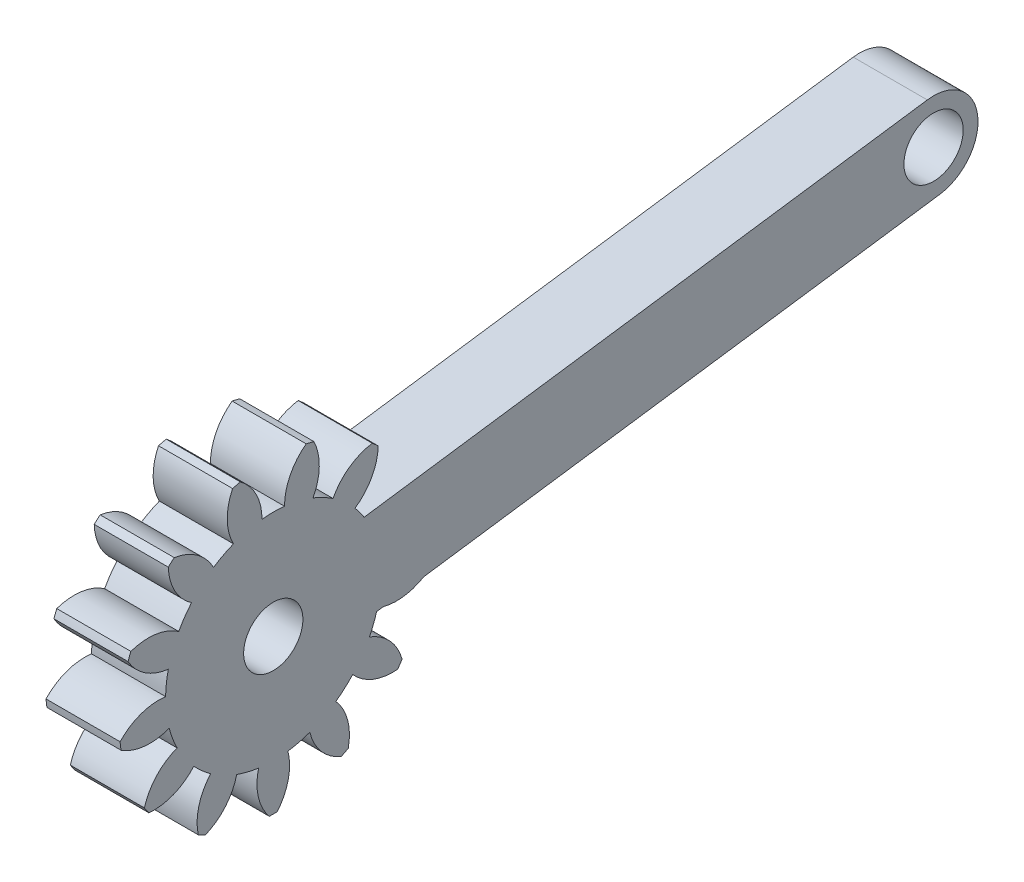
SolidWorks part; units mm, degrees
ref_plane "Front Plane" through (0, 0, 0) normal (0, 0, 1) x (1, 0, 0)
ref_plane "Top Plane" through (0, 0, 0) normal (0, 1, 0) x (1, 0, 0)
ref_plane "Right Plane" through (0, 0, 0) normal (1, 0, 0) x (0, 0, -1)
ref_plane "Plane1" through (-2.7128, 0, 0) normal (1, 0, 0) x (0, 0, -1)
sketch "Sketch1" plane through (-2.7128, 0, 0) normal (1, 0, 0) x (0, 0, -1)
  circle A0 centre (-74.3928, 33.7527) radius 2
  arc A1 (-81.4756, 41.3436) -> (-79.9078, 38.4838) centre (-77.8783, 41.4561) ccw
  arc A2 (-79.9078, 38.4838) -> (-80.7721, 37.2317) centre (-74.3928, 33.7527) ccw
  arc A3 (-80.7721, 37.2317) -> (-84.0021, 37.6835) centre (-82.8316, 34.28) ccw
  arc A4 (-84.0021, 37.6835) -> (-84.192, 37.1826) centre (-74.3928, 33.7527) ccw
  arc A5 (-84.192, 37.1826) -> (-81.4748, 35.3789) centre (-81.059, 38.9539) ccw
  arc A6 (-81.4748, 35.3789) -> (-81.6582, 33.8686) centre (-74.3928, 33.7527) ccw
  arc A7 (-81.6582, 33.8686) -> (-84.7281, 32.7676) centre (-82.11, 30.2979) ccw
  arc A8 (-84.7281, 32.7676) -> (-84.6635, 32.2358) centre (-74.3928, 33.7527) ccw
  arc A9 (-84.6635, 32.2358) -> (-81.4193, 31.9015) centre (-82.7125, 35.2603) ccw
  arc A10 (-81.4193, 31.9015) -> (-80.8798, 30.4789) centre (-74.3928, 33.7527) ccw
  arc A11 (-80.8798, 30.4789) -> (-83.0864, 28.0774) centre (-79.6205, 27.1073) ccw
  arc A12 (-83.0864, 28.0774) -> (-82.7821, 27.6366) centre (-74.3928, 33.7527) ccw
  arc A13 (-82.7821, 27.6366) -> (-79.7542, 28.8482) centre (-82.4602, 31.2212) ccw
  arc A14 (-79.7542, 28.8482) -> (-78.6154, 27.8393) centre (-74.3928, 33.7527) ccw
  arc A15 (-78.6154, 27.8393) -> (-79.4532, 24.6874) centre (-75.9334, 25.4391) ccw
  arc A16 (-79.4532, 24.6874) -> (-78.9789, 24.4384) centre (-74.3928, 33.7527) ccw
  arc A17 (-78.9789, 24.4384) -> (-76.8608, 26.9185) centre (-80.3597, 27.7621) ccw
  arc A18 (-76.8608, 26.9185) -> (-75.3836, 26.5543) centre (-74.3928, 33.7527) ccw
  arc A19 (-75.3836, 26.5543) -> (-74.6607, 23.3741) centre (-71.8934, 25.6754) ccw
  arc A20 (-74.6607, 23.3741) -> (-74.125, 23.3741) centre (-74.3928, 33.7527) ccw
  arc A21 (-74.125, 23.3741) -> (-73.4021, 26.5543) centre (-76.8923, 25.6754) ccw
  arc A22 (-73.4021, 26.5543) -> (-71.9249, 26.9185) centre (-74.3928, 33.7527) ccw
  arc A23 (-71.9249, 26.9185) -> (-69.8068, 24.4384) centre (-68.426, 27.7621) ccw
  arc A24 (-69.8068, 24.4384) -> (-69.3325, 24.6874) centre (-74.3928, 33.7527) ccw
  arc A25 (-69.3325, 24.6874) -> (-70.1703, 27.8393) centre (-72.8522, 25.4391) ccw
  arc A26 (-70.1703, 27.8393) -> (-69.0315, 28.8482) centre (-74.3928, 33.7527) ccw
  arc A27 (-69.0315, 28.8482) -> (-66.0036, 27.6366) centre (-66.3255, 31.2212) ccw
  arc A28 (-66.0036, 27.6366) -> (-65.6993, 28.0774) centre (-74.3928, 33.7527) ccw
  arc A29 (-65.6993, 28.0774) -> (-67.9059, 30.4789) centre (-69.1652, 27.1073) ccw
  arc A30 (-67.9059, 30.4789) -> (-67.3664, 31.9015) centre (-74.3928, 33.7527) ccw
  arc A31 (-67.3664, 31.9015) -> (-64.1222, 32.2358) centre (-66.0732, 35.2603) ccw
  arc A32 (-64.1222, 32.2358) -> (-64.0576, 32.7676) centre (-74.3928, 33.7527) ccw
  arc A33 (-64.0576, 32.7676) -> (-67.1275, 33.8686) centre (-66.6757, 30.2979) ccw
  arc A34 (-67.1275, 33.8686) -> (-67.3109, 35.3789) centre (-74.3928, 33.7527) ccw
  arc A35 (-67.3109, 35.3789) -> (-64.5937, 37.1826) centre (-67.7267, 38.9539) ccw
  arc A36 (-64.5937, 37.1826) -> (-64.7836, 37.6835) centre (-74.3928, 33.7527) ccw
  arc A37 (-64.7836, 37.6835) -> (-68.0136, 37.2317) centre (-65.9541, 34.28) ccw
  arc A38 (-68.0136, 37.2317) -> (-68.8779, 38.4838) centre (-74.3928, 33.7527) ccw
  arc A39 (-68.8779, 38.4838) -> (-67.3101, 41.3436) centre (-70.9074, 41.4561) ccw
  arc A40 (-67.3101, 41.3436) -> (-67.711, 41.6988) centre (-74.3928, 33.7527) ccw
  arc A41 (-67.711, 41.6988) -> (-70.361, 39.7978) centre (-67.1658, 38.1413) ccw
  arc A42 (-70.361, 39.7978) -> (-71.7082, 40.5048) centre (-74.3928, 33.7527) ccw
  arc A43 (-71.7082, 40.5048) -> (-71.649, 43.7657) centre (-74.8866, 42.1935) ccw
  arc A44 (-71.649, 43.7657) -> (-72.1691, 43.8938) centre (-74.3928, 33.7527) ccw
  arc A45 (-72.1691, 43.8938) -> (-73.6321, 40.979) centre (-70.033, 40.9972) ccw
  arc A46 (-73.6321, 40.979) -> (-75.1536, 40.979) centre (-74.3928, 33.7527) ccw
  arc A47 (-75.1536, 40.979) -> (-76.6166, 43.8938) centre (-78.7526, 40.9972) ccw
  arc A48 (-76.6166, 43.8938) -> (-77.1367, 43.7657) centre (-74.3928, 33.7527) ccw
  arc A49 (-77.1367, 43.7657) -> (-77.0775, 40.5048) centre (-73.8991, 42.1935) ccw
  arc A50 (-77.0775, 40.5048) -> (-78.4247, 39.7978) centre (-74.3928, 33.7527) ccw
  arc A51 (-78.4247, 39.7978) -> (-81.0747, 41.6988) centre (-81.6199, 38.1413) ccw
  arc A52 (-81.0747, 41.6988) -> (-81.4756, 41.3436) centre (-74.3928, 33.7527) ccw
  dimension "D1" = 4
extrude "Boss-Extrude1" add sketch "Sketch1" against normal blind 5
sketch "Sketch2" plane through (-2.7128, 0, 0) normal (1, 0, 0) x (0, 0, -1)
  line L0 (-74.3928, 33.7527) -> (-29.8382, 40.068) construction
  line L1 (-74.8139, 36.723) -> (-30.2592, 43.0383) construction
  line L2 (-73.9718, 30.7824) -> (-29.4172, 37.0977) construction
  line L3 (-74.8139, 36.723) -> (-30.2592, 43.0383)
  line L4 (-73.9718, 30.7824) -> (-29.4172, 37.0977)
  arc A0 (-74.8139, 36.723) -> (-73.9718, 30.7824) centre (-74.3928, 33.7527) ccw construction
  arc A1 (-29.4172, 37.0977) -> (-30.2592, 43.0383) centre (-29.8382, 40.068) ccw construction
  circle A2 centre (-29.8382, 40.068) radius 2
  arc A4 (-74.8139, 36.723) -> (-73.9718, 30.7824) centre (-74.3928, 33.7527) cw
  arc A5 (-30.2592, 43.0383) -> (-29.4172, 37.0977) centre (-29.8382, 40.068) cw
  point P2 (-52.1155, 36.9103)
  dimension "D2" = 4
  dimension "D1" = 6
  dimension "D3" = 45
extrude "Boss-Extrude2" add sketch "Sketch2" against normal blind 5
